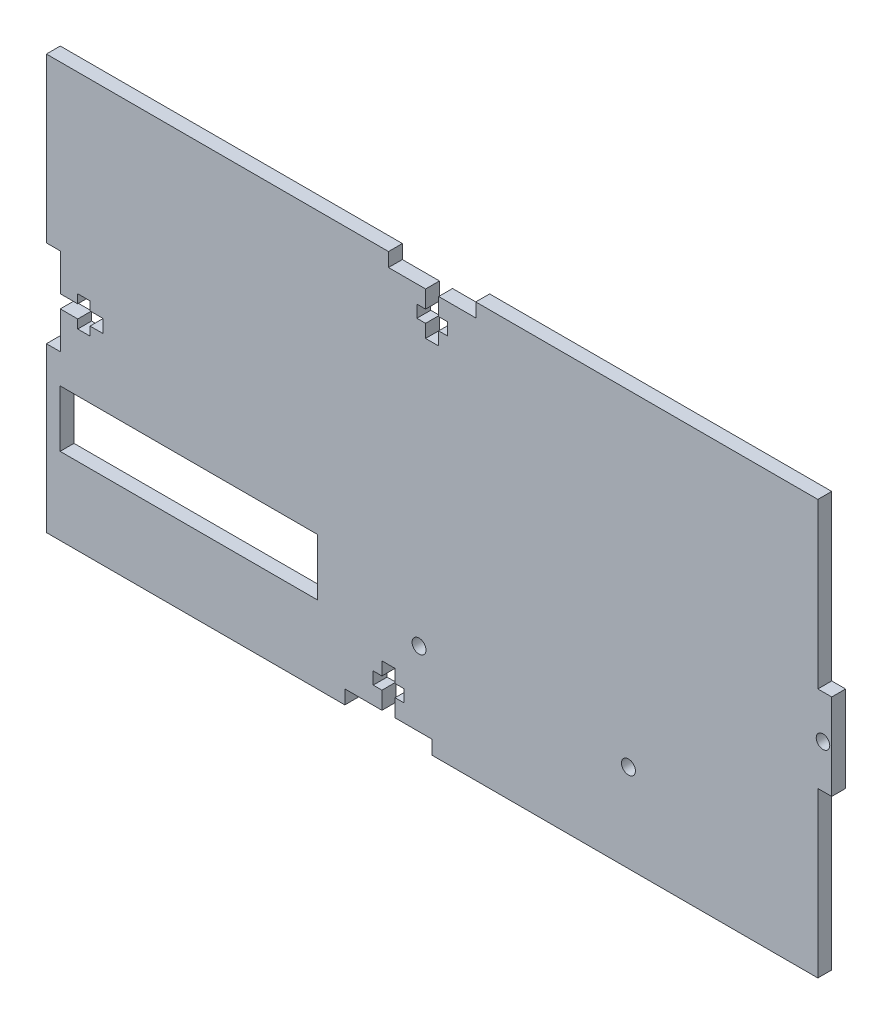
SolidWorks part; units mm, degrees
ref_plane "Front Plane" through (0, 0, 0) normal (0, 0, 1) x (1, 0, 0)
ref_plane "Top Plane" through (0, 0, 0) normal (0, 1, 0) x (1, 0, 0)
ref_plane "Right Plane" through (0, 0, 0) normal (1, 0, 0) x (0, 0, -1)
sketch "Sketch1" plane through (0, 0, 0) normal (0, 0, 1) x (1, 0, 0)
  line L1 (-90, 47.5) -> (90, 47.5)
  line L2 (-90, 47.5) -> (-90, -47.5)
  line L3 (-90, -47.5) -> (90, -47.5)
  line L4 (90, 47.5) -> (90, -47.5)
  point P0 (0, 0)
  dimension "D1" = 180
  dimension "D2" = 95
  dimension "D3" = 47.5
  dimension "D4" = 90
extrude "Boss-Extrude1" add sketch "Sketch1" along normal blind 3.18
sketch "Sketch2" plane through (0, 0, 3.18) normal (0, 0, 1) x (1, 0, 0)
  line L1 (90, 47.5) -> (86.82, 47.5)
  line L2 (90, 47.5) -> (90, 9.875)
  line L3 (90, 9.875) -> (86.82, 9.875)
  line L4 (86.82, 47.5) -> (86.82, 9.875)
  line L5 (90, -47.5) -> (86.82, -47.5)
  line L6 (90, -47.5) -> (90, -9.875)
  line L7 (90, -9.875) -> (86.82, -9.875)
  line L8 (86.82, -47.5) -> (86.82, -9.875)
  dimension "D1" = 3.18
  dimension "D2" = 37.625
  dimension "D3" = 37.625
  dimension "D4" = 3.18
extrude "Cut-Extrude1" cut sketch "Sketch2" against normal through all both and the other way through all
sketch "Sketch3" plane through (0, 0, 3.18) normal (0, 0, 1) x (1, 0, 0)
  line L0 (0, 0) -> (50000, 0) construction
  line L1 (0, 0) -> (0, 50000) construction
  line L2 (90, -9.875) -> (90, 9.875) construction
  circle A0 centre (88, 0) radius 1.55
  dimension "D1" = 3.1
  dimension "D2" = 2
extrude "Cut-Extrude2" cut sketch "Sketch3" against normal through all both and the other way through all
ref_plane "Plane1" through (-90, 47.5, 3.18) normal (-1, 0, 0) x (0, 0, 1)
sketch "Sketch5" plane through (0, 0, 0) normal (0, 0, -1) x (-1, 0, 0)
  line L0 (-86.82, 47.5) -> (90, 47.5) construction
  line L1 (11.59, 47.5) -> (-8.41, 47.5)
  line L2 (11.59, 47.5) -> (11.59, 44.32)
  line L3 (11.59, 44.32) -> (3.09, 44.32)
  line L4 (-8.41, 47.5) -> (-8.41, 44.32)
  line L5 (90, -1.1255) -> (90, 96.1255) construction
  line L7 (0.09, 44.32) -> (-8.41, 44.32)
  line L9 (3.09, 44.32) -> (3.09, 40.32)
  line L10 (3.09, 34.5) -> (0.09, 34.5)
  line L11 (0.09, 44.32) -> (0.09, 40.32)
  line L12 (5.09, 40.32) -> (3.09, 40.32)
  line L13 (5.09, 40.32) -> (5.09, 37.5)
  line L14 (5.09, 37.5) -> (3.09, 37.5)
  line L15 (-1.91, 40.32) -> (-1.91, 37.5)
  line L16 (0.09, 40.32) -> (-1.91, 40.32)
  line L17 (3.09, 37.5) -> (3.09, 34.5)
  line L18 (0.09, 37.5) -> (0.09, 34.5)
  line L19 (0.09, 37.5) -> (-1.91, 37.5)
  point P6 (11.59, 45.91)
  dimension "D1" = 20
  dimension "D2" = 3.18
  dimension "D3" = 78.41
  dimension "D4" = 9.82
  dimension "D5" = 3
  dimension "D6" = 8.5
  dimension "D7" = 7
  dimension "D8" = 2.82
  dimension "D9" = 2
  dimension "D10" = 4
extrude "Cut-Extrude3" cut sketch "Sketch5" against normal through all both and the other way through all
sketch "Sketch6" plane through (0, 0, 3.18) normal (0, 0, 1) x (1, 0, 0)
  line L0 (-90, -47.5) -> (86.82, -47.5) construction
  line L1 (-21.59, -47.5) -> (-1.59, -47.5)
  line L2 (-21.59, -47.5) -> (-21.59, -44.32)
  line L3 (-21.59, -44.32) -> (-13.09, -44.32)
  line L4 (-1.59, -47.5) -> (-1.59, -44.32)
  line L5 (-90, 47.5) -> (-90, -47.5) construction
  line L8 (-10.09, -44.32) -> (-1.59, -44.32)
  line L10 (-13.09, -44.32) -> (-13.09, -40.32)
  line L11 (-13.09, -34.5) -> (-10.09, -34.5)
  line L12 (-10.09, -44.32) -> (-10.09, -40.32)
  line L13 (-15.09, -37.5) -> (-13.09, -37.5)
  line L14 (-15.09, -37.5) -> (-15.09, -40.32)
  line L15 (-15.09, -40.32) -> (-13.09, -40.32)
  line L16 (-8.09, -37.5) -> (-8.09, -40.32)
  line L17 (-10.09, -40.32) -> (-8.09, -40.32)
  line L18 (-10.09, -37.5) -> (-8.09, -37.5)
  line L19 (-10.09, -37.5) -> (-10.09, -34.5)
  line L20 (-13.09, -37.5) -> (-13.09, -34.5)
  dimension "D1" = 20
  dimension "D2" = 3.18
  dimension "D3" = 68.41
  dimension "D4" = 9.82
  dimension "D5" = 3
  dimension "D6" = 8.5
  dimension "D7" = 7
  dimension "D8" = 2.82
  dimension "D9" = 2
  dimension "D10" = 3
extrude "Cut-Extrude4" cut sketch "Sketch6" against normal through all both and the other way through all
sketch "Sketch7" plane through (0, 0, 3.18) normal (0, 0, 1) x (1, 0, 0)
  line L0 (-90, 47.5) -> (-90, -47.5) construction
  line L1 (-90, 10) -> (-86.82, 10)
  line L2 (-90, 10) -> (-90, -10)
  line L3 (-90, -10) -> (-86.82, -10)
  line L4 (-86.82, 10) -> (-86.82, 1.5)
  line L5 (-86.82, -1.5) -> (-86.82, -10)
  line L6 (-86.82, 1.5) -> (-82.82, 1.5)
  line L8 (-86.82, -1.5) -> (-82.82, -1.5)
  line L9 (-77, 1.5) -> (-77, -1.5)
  line L10 (-82.82, 3.5) -> (-80, 3.5)
  line L11 (-82.82, 3.5) -> (-82.82, 1.5)
  line L12 (-82.82, -3.5) -> (-80, -3.5)
  line L13 (-80, 3.5) -> (-80, 1.5)
  line L14 (-82.82, -1.5) -> (-82.82, -3.5)
  line L15 (-80, 1.5) -> (-77, 1.5)
  line L16 (-80, -1.5) -> (-80, -3.5)
  line L17 (-80, -1.5) -> (-77, -1.5)
  dimension "D1" = 3.18
  dimension "D2" = 20
  dimension "D3" = 10
  dimension "D4" = 9.82
  dimension "D5" = 3
  dimension "D6" = 8.5
  dimension "D7" = 2.82
  dimension "D8" = 7
  dimension "D9" = 6.5
  dimension "D10" = 4
extrude "Cut-Extrude5" cut sketch "Sketch7" against normal through all both and the other way through all
sketch "Sketch8" plane through (0, 0, 3.18) normal (0, 0, 1) x (1, 0, 0)
  line L0 (-90, -10) -> (-90, -47.5) construction
  line L1 (-86.8548, -29.8) -> (-27.86, -29.8)
  line L2 (-86.8548, -29.8) -> (-86.8548, -16.8)
  line L3 (-86.8548, -16.8) -> (-27.86, -16.8)
  line L4 (-27.86, -29.8) -> (-27.86, -16.8)
  line L5 (-90, -47.5) -> (-21.59, -47.5) construction
  dimension "D1" = 58.9948
  dimension "D2" = 13
  dimension "D3" = 3.1452
  dimension "D4" = 17.7
extrude "Cut-Extrude6" cut sketch "Sketch8" against normal through all both and the other way through all
sketch "Sketch9" plane through (0, 0, 3.18) normal (0, 0, 1) x (1, 0, 0)
  circle A0 centre (-4.59, -27.32) radius 1.6
  circle A1 centre (43.41, -27.32) radius 1.6
  dimension "D1" = 3.2
  dimension "D2" = 3.2
extrude "Cut-Extrude7" cut sketch "Sketch9" against normal through all both and the other way through all
